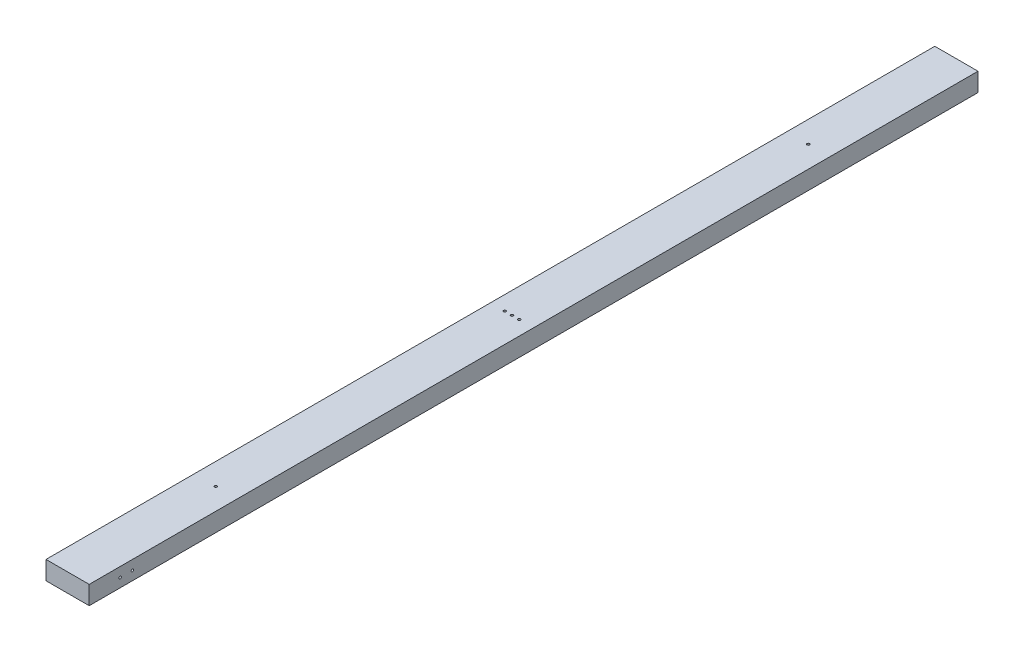
SolidWorks part; units mm, degrees
ref_plane "Front Plane" through (0, 0, 0) normal (0, 0, 1) x (1, 0, 0)
ref_plane "Top Plane" through (0, 0, 0) normal (0, 1, 0) x (1, 0, 0)
ref_plane "Right Plane" through (0, 0, 0) normal (1, 0, 0) x (0, 0, -1)
sketch "Sketch1" plane through (0, 0, 0) normal (0, 0, 1) x (1, 0, 0)
  line L1 (-24.2291, 19.8034) -> (64.6709, 19.8034)
  line L2 (-24.2291, 19.8034) -> (-24.2291, -18.2966)
  line L3 (-24.2291, -18.2966) -> (64.6709, -18.2966)
  line L4 (64.6709, 19.8034) -> (64.6709, -18.2966)
  dimension "D1" = 38.1
  dimension "D2" = 88.9
extrude "Boss-Extrude1" add sketch "Sketch1" along normal blind 1828.8
sketch "Sketch2" plane through (-24.2291, 0, 0) normal (-1, 0, 0) x (0, 0, 1)
  circle A0 centre (1739.9, 0) radius 2.5797
  circle A1 centre (1765.3, 0) radius 2.5797
  point P3 (1739.9, 0)
  point P4 (1765.3, 0)
  dimension "D4" = 5.1594
  dimension "D5" = 5.1594
extrude "Cut-Extrude1" cut sketch "Sketch2" against normal through all
sketch "Sketch3" plane through (0, -18.2966, 0) normal (0, -1, 0) x (1, 0, 0)
  line L0 (64.6709, 1828.8) -> (64.6709, 0) construction
  line L1 (-24.2291, 1828.8) -> (-24.2291, 0) construction
  line L2 (-24.2291, 1828.8) -> (64.6709, 1828.8) construction
  circle A0 centre (35.0375, 914.4) radius 2.5797
  circle A1 centre (5.4042, 914.4) radius 2.5797
  dimension "D3" = 5.1594
  dimension "D4" = 5.1594
  dimension "D1" = 29.6333
  dimension "D2" = 29.6333
extrude "Cut-Extrude2" cut sketch "Sketch3" against normal through all
sketch "Sketch4" plane through (0, -18.2966, 0) normal (0, -1, 0) x (1, 0, 0)
  line L0 (-24.2291, 1828.8) -> (64.6709, 1828.8) construction
  line L1 (64.6709, 1828.8) -> (64.6709, 0) construction
  line L2 (-24.2291, 1828.8) -> (-24.2291, 0) construction
  line L3 (-24.2291, 0) -> (64.6709, 0) construction
  circle A0 centre (20.2209, 1524) radius 2.5797
  circle A1 centre (20.2209, 914.4) radius 2.5797
  circle A2 centre (20.2209, 304.8) radius 2.5797
  dimension "D3" = 5.1594
  dimension "D6" = 5.1594
  dimension "D7" = 5.1594
  dimension "D1" = 304.8
  dimension "D2" = 44.45
  dimension "D4" = 44.45
  dimension "D5" = 914.4
  dimension "D8" = 44.45
  dimension "D9" = 304.8
extrude "Cut-Extrude3" cut sketch "Sketch4" against normal through all
